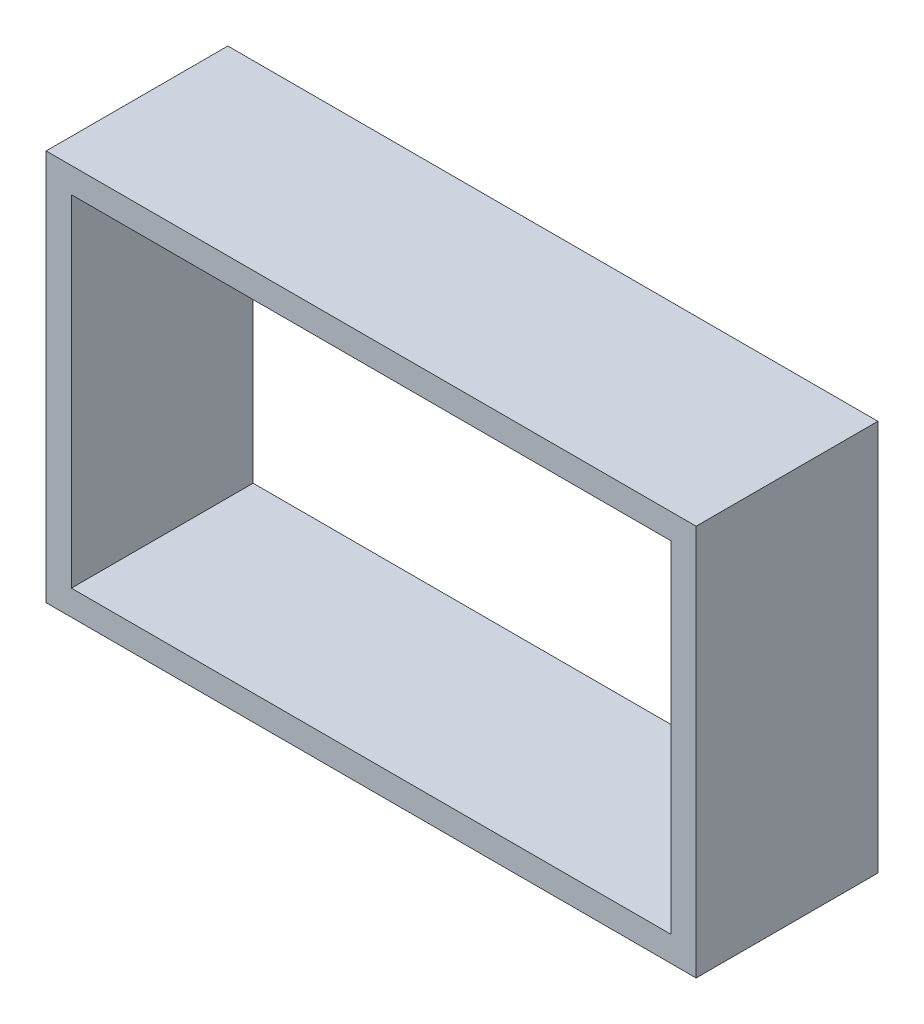
SolidWorks part; units mm, degrees
ref_plane "Alzado" through (0, 0, 0) normal (0, 0, 1) x (1, 0, 0)
ref_plane "Planta" through (0, 0, 0) normal (0, 1, 0) x (1, 0, 0)
ref_plane "Vista lateral" through (0, 0, 0) normal (1, 0, 0) x (0, 0, -1)
sketch "Croquis1" plane through (0, 0, 0) normal (0, 0, 1) x (1, 0, 0)
  line L1 (-71.7344, 18.0156) -> (-24.2344, 18.0156)
  line L2 (-71.7344, 18.0156) -> (-71.7344, -8.9844)
  line L3 (-71.7344, -8.9844) -> (-24.2344, -8.9844)
  line L4 (-24.2344, 18.0156) -> (-24.2344, -8.9844)
  line L5 (-73.7344, 20.0156) -> (-22.2344, 20.0156)
  line L6 (-73.7344, 20.0156) -> (-73.7344, -10.9844)
  line L7 (-73.7344, -10.9844) -> (-22.2344, -10.9844)
  line L8 (-22.2344, 20.0156) -> (-22.2344, -10.9844)
  dimension "D1" = 47.5
  dimension "D2" = 27
  dimension "D3" = 2
  dimension "D4" = 2
  dimension "D5" = 2
  dimension "D6" = 2
extrude "Saliente-Extruir1" add sketch "Croquis1" along normal blind 14.4
